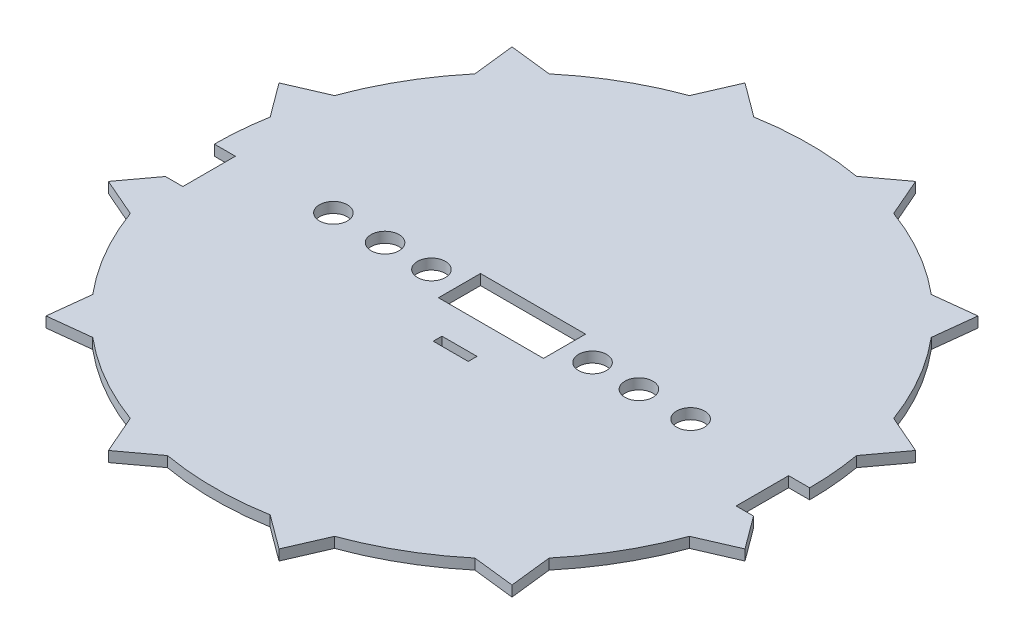
SolidWorks part; units mm, degrees
material "Ceramic Porcelain"
ref_plane "Front Plane" through (0, 0, 0) normal (0, 0, 1) x (1, 0, 0)
ref_plane "Top Plane" through (0, 0, 0) normal (0, 1, 0) x (1, 0, 0)
ref_plane "Right Plane" through (0, 0, 0) normal (1, 0, 0) x (0, 0, -1)
sketch "Sketch1" plane through (0, 0, 0) normal (0, 1, 0) x (1, 0, 0)
  line L0 (0, 0) -> (-2.4355, 9.0894) construction
  line L1 (0, -55) -> (0, 55) construction
  line L2 (-2.4355, 9.0894) -> (-2.9158, 7.9842)
  line L3 (-2.4355, 9.0894) -> (-1.4669, 8.3725)
  line L4 (2.4355, 9.0894) -> (1.4669, 8.3725)
  line L5 (2.4355, 9.0894) -> (2.9158, 7.9842)
  line L6 (0, 0) -> (2.4355, 9.0894) construction
  line L7 (6.6539, 6.6539) -> (5.4566, 6.5173)
  line L8 (6.6539, 6.6539) -> (6.5173, 5.4566)
  line L9 (0, 0) -> (6.6539, 6.6539) construction
  line L10 (9.0894, 2.4355) -> (7.9842, 2.9158)
  line L11 (9.0894, 2.4355) -> (8.3725, 1.4669)
  line L12 (0, 0) -> (9.0894, 2.4355) construction
  line L13 (9.0894, -2.4355) -> (8.3725, -1.4669)
  line L14 (9.0894, -2.4355) -> (7.9842, -2.9158)
  line L15 (0, 0) -> (9.0894, -2.4355) construction
  line L16 (6.6539, -6.6539) -> (6.5173, -5.4566)
  line L17 (6.6539, -6.6539) -> (5.4566, -6.5173)
  line L18 (0, 0) -> (6.6539, -6.6539) construction
  line L19 (2.4355, -9.0894) -> (2.9158, -7.9842)
  line L20 (2.4355, -9.0894) -> (1.4669, -8.3725)
  line L21 (0, 0) -> (2.4355, -9.0894) construction
  line L22 (-2.4355, -9.0894) -> (-1.4669, -8.3725)
  line L23 (-2.4355, -9.0894) -> (-2.9158, -7.9842)
  line L24 (0, 0) -> (-2.4355, -9.0894) construction
  line L25 (-6.6539, -6.6539) -> (-5.4566, -6.5173)
  line L26 (-6.6539, -6.6539) -> (-6.5173, -5.4566)
  line L27 (0, 0) -> (-6.6539, -6.6539) construction
  line L28 (-9.0894, -2.4355) -> (-7.9842, -2.9158)
  line L29 (-9.0894, -2.4355) -> (-8.3725, -1.4669)
  line L30 (0, 0) -> (-9.0894, -2.4355) construction
  line L31 (-9.0894, 2.4355) -> (-8.3725, 1.4669)
  line L32 (-9.0894, 2.4355) -> (-7.9842, 2.9158)
  line L33 (0, 0) -> (-9.0894, 2.4355) construction
  line L34 (-6.6539, 6.6539) -> (-6.5173, 5.4566)
  line L35 (-6.6539, 6.6539) -> (-5.4566, 6.5173)
  line L36 (0, 0) -> (-6.6539, 6.6539) construction
  arc A0 (-2.9158, 7.9842) -> (-5.4566, 6.5173) centre (0, 0) ccw
  circle A1 centre (0, 0) radius 9.41 construction
  arc A2 (1.4669, 8.3725) -> (-1.4669, 8.3725) centre (0, 0) ccw
  arc A3 (5.4566, 6.5173) -> (2.9158, 7.9842) centre (0, 0) ccw
  arc A4 (7.9842, 2.9158) -> (6.5173, 5.4566) centre (0, 0) ccw
  arc A5 (8.3725, -1.4669) -> (8.3725, 1.4669) centre (0, 0) ccw
  arc A6 (6.5173, -5.4566) -> (7.9842, -2.9158) centre (0, 0) ccw
  arc A7 (2.9158, -7.9842) -> (5.4566, -6.5173) centre (0, 0) ccw
  arc A8 (-1.4669, -8.3725) -> (1.4669, -8.3725) centre (0, 0) ccw
  arc A9 (-5.4566, -6.5173) -> (-2.9158, -7.9842) centre (0, 0) ccw
  arc A10 (-7.9842, -2.9158) -> (-6.5173, -5.4566) centre (0, 0) ccw
  arc A11 (-8.3725, 1.4669) -> (-8.3725, -1.4669) centre (0, 0) ccw
  arc A12 (-6.5173, 5.4566) -> (-7.9842, 2.9158) centre (0, 0) ccw
  dimension "D1" = 17
  dimension "D2" = 18.82
  dimension "D3" = 15
  dimension "D4" = 1.5
extrude "Extrude1" add sketch "Sketch1" along normal blind 0.3
sketch "Sketch3" plane through (0, 0, 0) normal (0, 1, 0) x (1, 0, 0)
  line L0 (-0.703, 0) -> (0.703, 0) construction
  line L1 (0, -0.5846) -> (0, 0.5846) construction
  line L3 (-1.5, 0.6) -> (1.5, 0.6)
  line L4 (-1.5, 0.6) -> (-1.5, -0.6)
  line L5 (-1.5, -0.6) -> (1.5, -0.6)
  line L6 (1.5, 0.6) -> (1.5, -0.6)
  circle A0 centre (-2.3, 0) radius 0.4
  circle A1 centre (-3.625, 0) radius 0.4
  circle A2 centre (-5.1, 0) radius 0.4
  circle A3 centre (2.3, 0) radius 0.4
  circle A4 centre (3.625, 0) radius 0.4
  circle A5 centre (5.1, 0) radius 0.4
  dimension "D7" = 0.8
  dimension "D1" = 10.2
  dimension "D2" = 7.25
  dimension "D3" = 4.6
  dimension "D4" = 2.3
  dimension "D5" = 3.625
  dimension "D6" = 5.1
  dimension "D8" = 1.2
  dimension "D9" = 0.6
  dimension "D10" = 3
  dimension "D11" = 1.5
extrude "Extrude2" cut sketch "Sketch3" along normal through all
sketch "Sketch4" plane through (0, 0, 0) normal (0, 1, 0) x (1, 0, 0)
  line L0 (0, -0.5846) -> (0, 0.5846) construction
  line L1 (-0.5, -1.5) -> (0.5, -1.5)
  line L2 (-0.5, -1.5) -> (-0.5, -1.75)
  line L3 (-0.5, -1.75) -> (0.5, -1.75)
  line L4 (0.5, -1.5) -> (0.5, -1.75)
  line L5 (-0.703, 0) -> (0.703, 0) construction
  dimension "D1" = 1
  dimension "D2" = 0.5
  dimension "D3" = 0.25
  dimension "D4" = 1.5
extrude "Extrude3" cut sketch "Sketch4" along normal blind 24
sketch "Sketch5" plane through (0, 0, 0) normal (0, 1, 0) x (1, 0, 0)
  line L0 (-0.703, 0) -> (0.703, 0) construction
  line L1 (-9.4, 0) -> (-7.9, 0)
  line L2 (-9.4, 0) -> (-9.4, -1.5)
  line L3 (-9.4, -1.5) -> (-7.9, -1.5)
  line L4 (-7.9, 0) -> (-7.9, -1.5)
  line L5 (0, -0.5846) -> (0, 0.5846) construction
  line L6 (7.9, 0) -> (9.4, 0)
  line L7 (7.9, 0) -> (7.9, -1.5)
  line L8 (7.9, -1.5) -> (9.4, -1.5)
  line L9 (9.4, 0) -> (9.4, -1.5)
  dimension "D1" = 15.8
  dimension "D2" = 7.9
  dimension "D3" = 1.5
extrude "Extrude5" cut sketch "Sketch5" along normal blind 1
